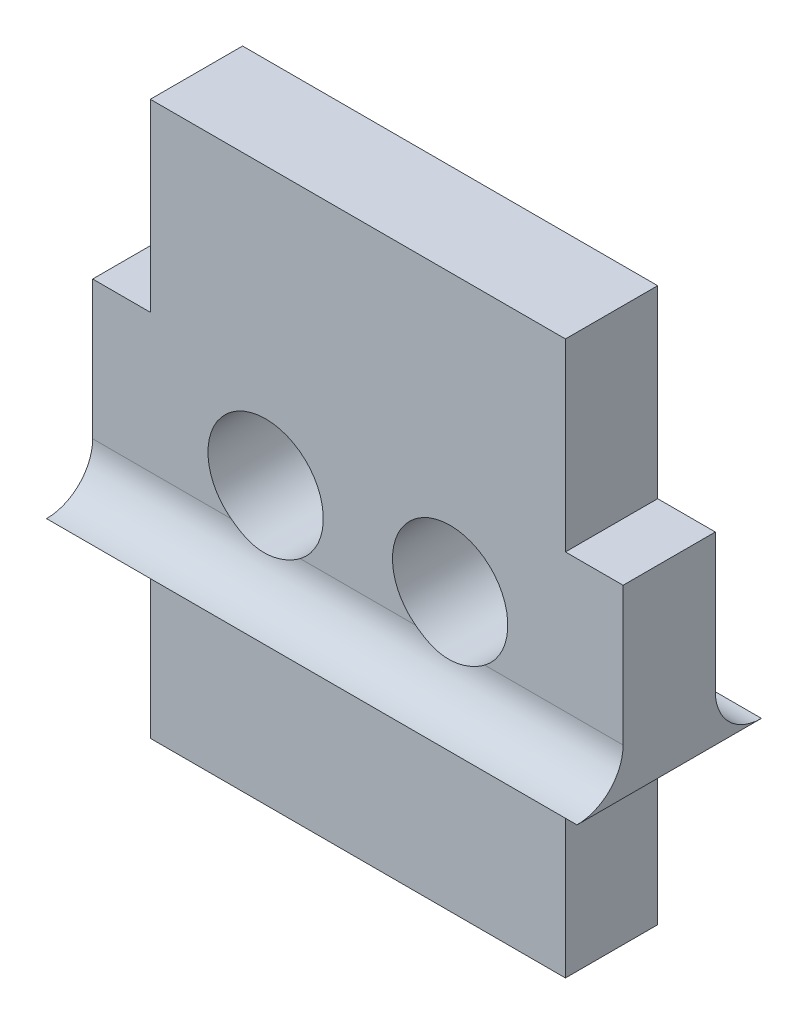
SolidWorks part; units mm, degrees
ref_plane "Front Plane" through (0, 0, 0) normal (0, 0, 1) x (1, 0, 0)
ref_plane "Top Plane" through (0, 0, 0) normal (0, 1, 0) x (1, 0, 0)
ref_plane "Right Plane" through (0, 0, 0) normal (1, 0, 0) x (0, 0, -1)
sketch "Model" plane through (0, 0, 0) normal (0, 0, 1) x (1, 0, 0)
  line L0 (5.7504, 12) -> (5.7504, 0) construction
  line L37 (1.25, 4) -> (0, 4)
  line L38 (10.2507, 4) -> (11.5007, 4)
  line L39 (1.25, 0) -> (10.2507, 0)
  line L40 (1.25, 4) -> (1.25, 0)
  line L41 (10.2507, 4) -> (10.2507, 0)
  line L126 (10.2507, 8) -> (11.5007, 8)
  line L127 (1.25, 8) -> (0, 8)
  line L128 (10.2507, 12) -> (1.25, 12)
  line L129 (10.2507, 8) -> (10.2507, 12)
  line L130 (1.25, 8) -> (1.25, 12)
  line L131 (0, 8) -> (0, 4)
  line L132 (11.5007, 8) -> (11.5007, 4)
  circle A81 centre (7.7507, 6) radius 1.25
  circle A82 centre (3.75, 6) radius 1.25
  dimension "D1" = 2.5
  dimension "D2" = 2
  dimension "D3" = 2.5
  dimension "D4" = 9.0007
  dimension "D5" = 4
  dimension "D6" = 2.5
extrude "Boss-Extrude1" add sketch "Model" along normal blind 2
sketch "Sketch1" plane through (0, 0, 0) normal (-1, 0, 0) x (0, 0, 1)
  line L0 (1, 0) -> (1, 7) construction
  line L1 (2, 4) -> (2, 5)
  line L2 (2, 4) -> (3, 4)
  line L3 (0, 4) -> (-1, 4)
  line L4 (0, 4) -> (0, 5)
  arc A0 (2, 5) -> (3, 4) centre (3, 5) ccw
  arc A1 (0, 5) -> (-1, 4) centre (-1, 5) cw
  dimension "D1" = 1
  dimension "D2" = 1
  dimension "D3" = 4
  dimension "D4" = 1
  dimension "D5" = 2
extrude "Boss-Extrude2" add sketch "Sketch1" against normal up to surface (11.5007 mm away) up to face at (11.5007, 6, 1)
sketch "Sketch2" plane through (0, 0, 2) normal (0, 0, 1) x (1, 0, 0)
  line L0 (5.7504, 12) -> (5.7504, 0) construction
  line L1 (10.2507, 12) -> (1.25, 12) construction
  line L2 (1.25, 0) -> (10.2507, 0) construction
  circle A0 centre (3.75, 6) radius 1.25
  circle A1 centre (7.7507, 6) radius 1.25
  dimension "D1" = 2.5
extrude "Cut-Extrude1" cut sketch "Sketch2" against normal through all both and the other way through all
equation "\"D4@Model\"= \"fingerWidth@parametersSketch@prostheticParameters.SLDPRT\" * 0.5556"
